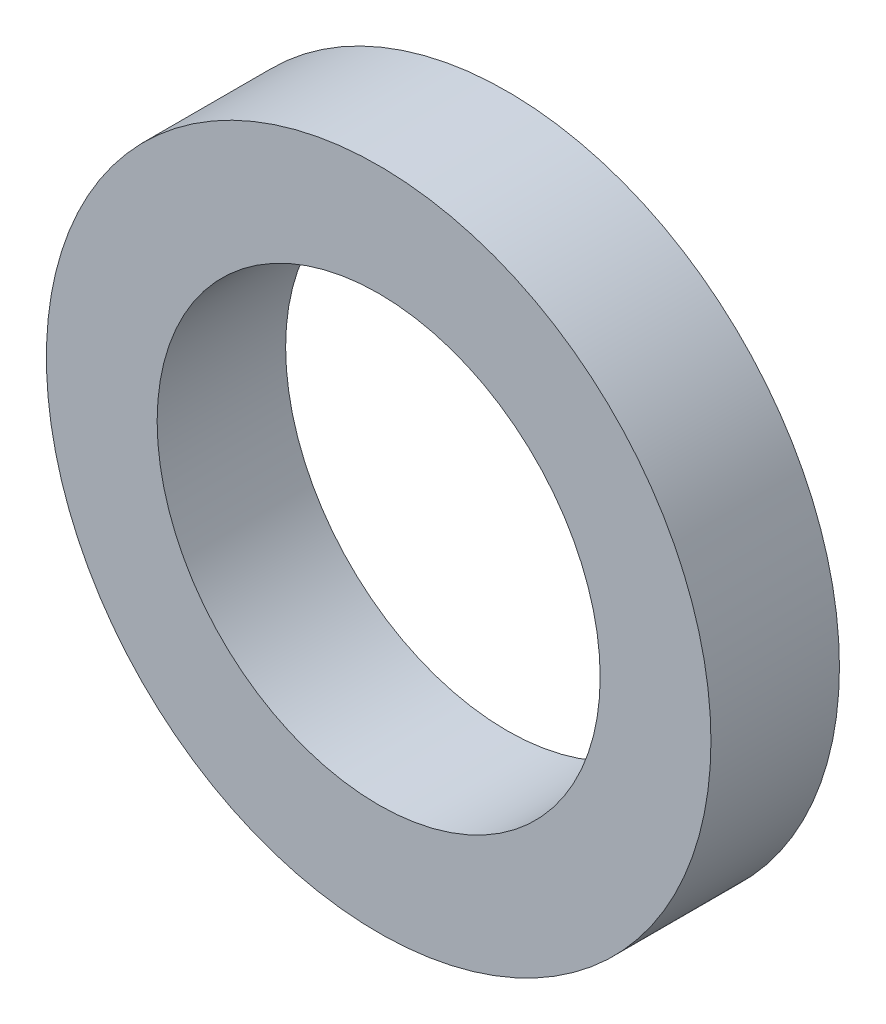
SolidWorks part; units mm, degrees
ref_plane "Front Plane" through (0, 0, 0) normal (0, 0, 1) x (1, 0, 0)
ref_plane "Top Plane" through (0, 0, 0) normal (0, 1, 0) x (1, 0, 0)
ref_plane "Right Plane" through (0, 0, 0) normal (1, 0, 0) x (0, 0, -1)
sketch "Sketch1" plane through (0, 0, 0) normal (0, 0, 1) x (1, 0, 0)
  circle A0 centre (0, 0) radius 6.35
  circle A1 centre (0, 0) radius 9.525
  dimension "D1" = 12.7
  dimension "D2" = 19.05
extrude "Boss-Extrude1" add sketch "Sketch1" along normal blind 3.683
